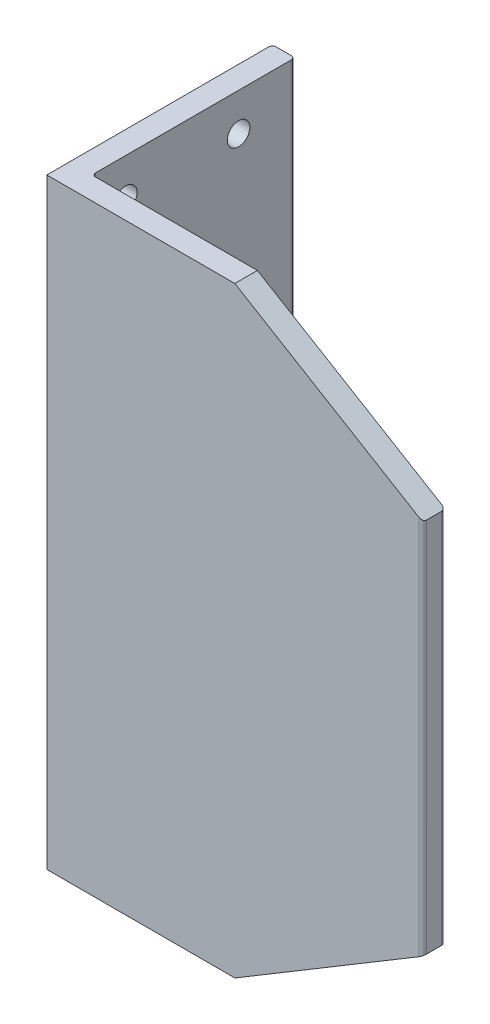
SolidWorks part; units mm, degrees
ref_plane "Front Plane" through (0, 0, 0) normal (0, 0, 1) x (1, 0, 0)
ref_plane "Top Plane" through (0, 0, 0) normal (0, 1, 0) x (1, 0, 0)
ref_plane "Right Plane" through (0, 0, 0) normal (1, 0, 0) x (0, 0, -1)
sketch "Sketch1" plane through (0, 0, 0) normal (0, 1, 0) x (1, 0, 0)
  line L0 (0, 0) -> (0, 59)
  line L1 (1, 60) -> (5, 60)
  line L2 (6, 59) -> (6, 7)
  line L3 (7, 6) -> (99, 6)
  line L4 (100, 5) -> (100, 1)
  line L5 (99, 0) -> (0, 0)
  arc A0 (100, 1) -> (99, 0) centre (99, 1) cw
  arc A1 (99, 6) -> (100, 5) centre (99, 5) cw
  arc A2 (6, 7) -> (7, 6) centre (7, 7) ccw
  arc A3 (5, 60) -> (6, 59) centre (5, 59) cw
  arc A4 (0, 59) -> (1, 60) centre (1, 59) cw
  point P9 (100, 0)
  point P12 (100, 6)
  point P17 (6, 60)
  point P20 (0, 60)
  dimension "D5" = 1
  dimension "D1" = 100
  dimension "D2" = 60
  dimension "D3" = 6
  dimension "D4" = 6
extrude "Boss-Extrude1" add sketch "Sketch1" along normal blind 160
ref_plane "Plane1" through (0, 80, 0) normal (0, 1, 0) x (1, 0, 0)
sketch "Sketch4" plane through (0, 80, 0) normal (0, 1, 0) x (1, 0, 0)
  line L0 (6, 59) -> (99, 6)
rib "Rib6" sketch "Sketch4" sketch "Sketch4" thickness 6 extrusion direction parallel to sketch draft on no parameters "D1"=6
sketch "Sketch5" plane through (0, 0, 0) normal (0, 0, 1) x (1, 0, 0)
  line L0 (100, 160) -> (50, 160)
  line L1 (0, 160) -> (99, 160) construction
  line L2 (50, 160) -> (100, 130)
  line L3 (100, 160) -> (100, 0) construction
  line L4 (100, 130) -> (100, 160)
  line L5 (-18.4643, 80) -> (129.2396, 80) construction
  line L6 (33, 80) -> (-33, 80) construction
  line L7 (100, 30) -> (100, 0)
  line L8 (50, 0) -> (100, 30)
  line L9 (100, 0) -> (50, 0)
  dimension "D1" = 50
  dimension "D2" = 30
extrude "Cut-Extrude1" cut sketch "Sketch5" against normal through all
sketch "Sketch6" plane through (0, 0, 0) normal (-1, 0, 0) x (0, 0, 1)
  line L0 (0, 160) -> (0, 0) construction
  line L1 (-60, 160) -> (-60, 0) construction
  line L2 (-59, 160) -> (0, 160) construction
  line L3 (-88.9511, 80) -> (36.1214, 80) construction
  line L5 (27.5, 80) -> (-27.5, 80) construction
  circle A0 centre (-45, 150) radius 3
  circle A1 centre (-15, 150) radius 3
  circle A2 centre (-15, 10) radius 3
  circle A3 centre (-45, 10) radius 3
  dimension "D1" = 6
  dimension "D2" = 6
  dimension "D3" = 15
  dimension "D4" = 15
  dimension "D5" = 10
  dimension "D6" = 10
extrude "Cut-Extrude2" cut sketch "Sketch6" against normal blind 10
